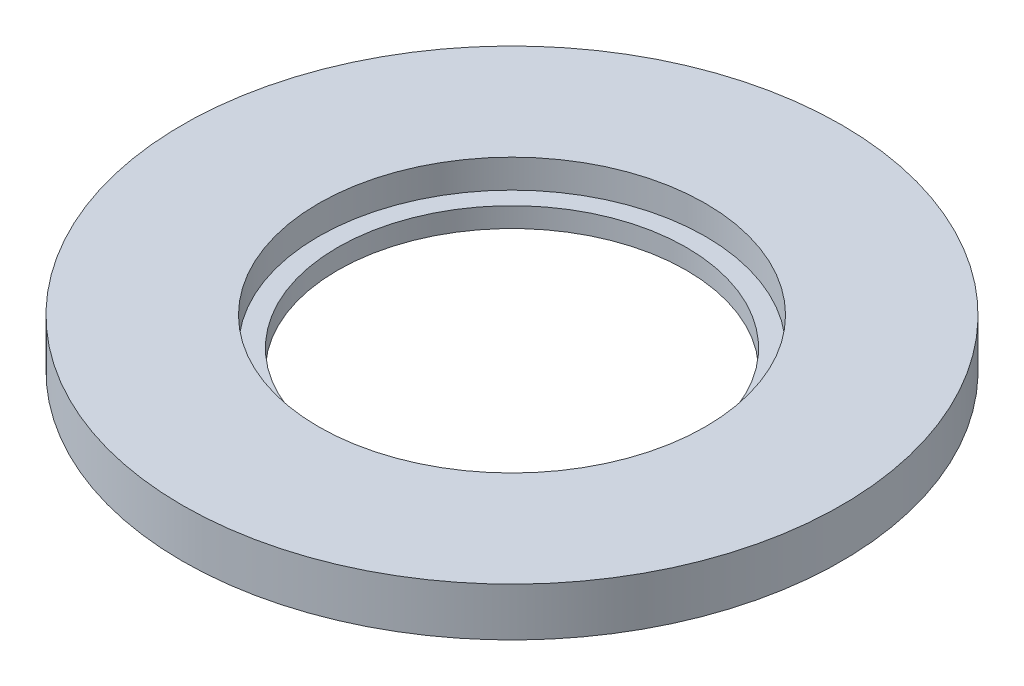
SolidWorks part; units mm, degrees
material "6061-T6 (SS)"
ref_plane "Front Plane" through (0, 0, 0) normal (0, 0, 1) x (1, 0, 0)
ref_plane "Top Plane" through (0, 0, 0) normal (0, 1, 0) x (1, 0, 0)
ref_plane "Right Plane" through (0, 0, 0) normal (1, 0, 0) x (0, 0, -1)
sketch "Sketch2" plane through (0, 0, 0) normal (1, 0, 0) x (0, 0, -1)
  line L0 (-45.8, 0) -> (-82.55, 0)
  line L1 (-82.55, 0) -> (-82.55, 12.7)
  line L2 (-82.55, 12.7) -> (-50.8, 12.7)
  line L3 (-45.8, 0) -> (-45.8, 5.2)
  line L4 (-45.8, 5.2) -> (-50.8, 5.2)
  line L5 (-50.8, 5.2) -> (-50.8, 12.7)
  line L6 (-80.2166, 12.7) -> (-80.2166, 0) construction
  dimension "D1" = 82.55
  dimension "D2" = 12.7
  dimension "D3" = 50.8
  dimension "D4" = 5
  dimension "D5" = 7.5
ref_axis "Axis1" through (0, -0.5, 0) along (0, 1, 0)
revolve "Revolve1" add sketch "Sketch2" angle 360 about axis through (0, -0.5, 0) along (0, 1, 0)
hole_wizard "#90 (0.0087) Diameter Hole1" [suppressed] positions "Sketch6" profile "Sketch7" hole size "#90" standard "ANSI Inch"
sketch "Sketch6" plane through (0, 12.7, 0) normal (0, 1, 0) x (1, 0, 0)
  line L0 (0, 0) -> (-69.8201, 120.932) construction
  line L2 (0, 0) -> (0, 109.0908) construction
  point P0 (-35, 60.6218)
  dimension "D1" = 30
  dimension "D2" = 70
sketch "Sketch7" plane through (-35, 12.7, -60.6218) normal (1, 0, 0) x (0, 0, 1)
  line L0 (0, 0) -> (0, 12.7)
  line L1 (0, 12.7) -> (0.1105, 12.7)
  line L2 (0.1105, 12.7) -> (0.1105, 0)
  line L5 (0.1105, 0) -> (0, 0)
  line L11 (0, -6.35) -> (0, 107.95) construction
  dimension "Thru Hole Dia." = 0.221
  dimension "Thru Hole Depth" = 12.7
pattern_circular "CirPattern3" [suppressed] count 3 over 360 about axis through (0, -0.5, 0) along (0, 1, 0)
sketch "Sketch8" [suppressed] plane through (0, 12.7, 0) normal (0, 1, 0) x (1, 0, 0)
  line L4 (0, 0) -> (46.9997, 81.4059) construction
  line L5 (-21.0255, 51.4172) -> (-32.098, 70.5955)
  line L6 (55.0414, 7.5) -> (77.1865, 7.5)
  line L7 (0, 0) -> (-35, 60.6218) construction
  arc A0 (-21.0255, 51.4172) -> (55.0414, 7.5) centre (0, 0) cw
  arc A1 (-32.098, 70.5955) -> (77.1865, 7.5) centre (0, 0) cw
  circle A2 centre (0, 0) radius 82.55 construction
  dimension "D1" = 27
  dimension "D2" = 5
  dimension "D3" = 7.5
  dimension "D4" = 60
extrude "Cut-Extrude1" [suppressed] cut sketch "Sketch8" against normal blind 10
fillet "Fillet1" [suppressed] radius 4
pattern_circular "CirPattern4" [suppressed] count 3 over 360 about axis through (0, -0.5, 0) along (0, 1, 0)
chamfer "Chamfer1" [suppressed] distance 4 angle 45
sketch "Sketch10" plane through (0, 0, 0) normal (0, -1, 0) x (1, 0, 0)
  circle A0 centre (0, 0) radius 82.55
  circle A1 centre (0, 0) radius 84.55
  circle A2 centre (0, 0) radius 82.55 construction
  dimension "D1" = 2
extrude "Boss-Extrude1" [suppressed] add sketch "Sketch10" against normal blind 7.5
chamfer "Chamfer3" [suppressed] distance 5 angle 60
fillet "Fillet4" [suppressed] radius 5
hole_wizard "CBORE for #6 Binding Head Machine Screw1" [suppressed] positions "Sketch13" profile "Sketch14" counterbore size "#6" standard "ANSI Inch"
sketch "Sketch13" [suppressed] plane through (0, 0, 0) normal (0, -1, 0) x (-1, 0, 0)
  point P4 (35, 60.6218)
sketch "Sketch14" plane through (-35, 0, -60.6218) normal (1, 0, 0) x (0, 0, -1)
  line L0 (0, 0) -> (0, 12.7)
  line L1 (0, 12.7) -> (1.8986, 12.7)
  line L3 (1.8986, 12.7) -> (1.8987, 2.2098)
  line L4 (1.8987, 2.2098) -> (3.9688, 2.2098)
  line L5 (3.9688, 2.2098) -> (3.9688, 0)
  line L7 (3.9688, 0) -> (0, 0)
  line L11 (0, -6.35) -> (0, 107.95) construction
  dimension "Thru Hole Dia." = 3.7973
  dimension "Thru Hole Depth" = 12.7
  dimension "C'Bore Dia." = 7.9375
  dimension "C'Bore Depth" = 2.2098
pattern_circular "CirPattern5" [suppressed] count 3 over 360 about axis through (0, -0.5, 0) along (0, 1, 0)
sketch "Sketch15" plane through (0, 0, 0) normal (0, -1, 0) x (1, 0, 0)
  circle A0 centre (0, 0) radius 82.55
  circle A1 centre (0, 0) radius 86.55
  circle A2 centre (0, 0) radius 82.55 construction
  dimension "D1" = 4
extrude "Boss-Extrude2" add sketch "Sketch15" against normal blind 12.7
equation "\"TubeDiameter\" = 6.500in"
